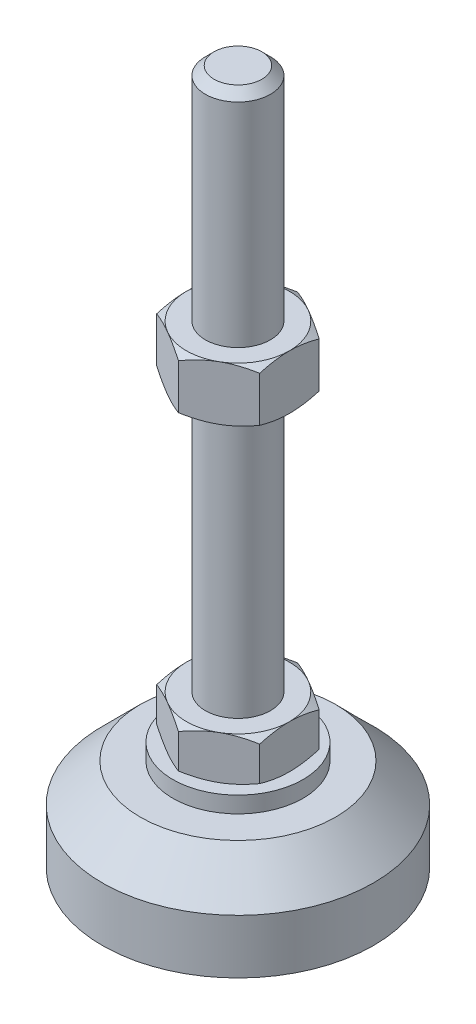
SolidWorks part; units mm, degrees
ref_plane "Спереди" through (0, 0, 0) normal (0, 0, 1) x (1, 0, 0)
ref_plane "Сверху" through (0, 0, 0) normal (0, 1, 0) x (1, 0, 0)
ref_plane "Справа" through (0, 0, 0) normal (1, 0, 0) x (0, 0, -1)
sketch "Эскиз1" plane through (0, 0, 0) normal (0, 0, 1) x (1, 0, 0)
  line L0 (0, 0) -> (-25, 0)
  line L3 (-25, 0) -> (-25, 10)
  line L5 (-12, 20) -> (-6, 20)
  line L12 (-6, 28) -> (-6, 126.4)
  line L13 (-6, 126.4) -> (-4.4, 128)
  line L14 (-4.4, 128) -> (0, 128)
  line L15 (0, 128) -> (0, 0) construction
  line L16 (-6, 20) -> (0, 20) construction
  line L17 (0, 0) -> (0, 128)
  line L18 (0, 0) -> (0, -7.9595) construction
  line L19 (-6, 28) -> (-6, 20)
  line L20 (-12, 20) -> (-12, 17)
  line L21 (-12, 17) -> (-18, 17)
  line L22 (-18, 17) -> (-25, 10)
  point P8 (-6, 77.2)
  point P23 (-9, 20)
  dimension "D1" = 12
  dimension "D2" = 20
  dimension "D3" = 8
  dimension "D4" = 50
  dimension "D5" = 6
  dimension "D6" = 1.6
  dimension "D7" = 45
  dimension "D8" = 24
  dimension "D10" = 100
  dimension "D11" = 10
  dimension "D12" = 45
  dimension "D13" = 3
revolve "Повернуть1" add sketch "Эскиз1" angle 360 about L17
sketch "Эскиз2" plane through (0, 20, 0) normal (0, 1, 0) x (1, 0, 0)
  line L1 (0, 10.9697) -> (-9.5, 5.4848)
  line L2 (-9.5, 5.4848) -> (-9.5, -5.4848)
  line L3 (-9.5, -5.4848) -> (0, -10.9697)
  line L4 (0, -10.9697) -> (9.5, -5.4848)
  line L5 (9.5, -5.4848) -> (9.5, 5.4848)
  line L6 (9.5, 5.4848) -> (0, 10.9697)
  circle A0 centre (0, 0) radius 9.5 construction
  dimension "D1" = 19
extrude "Бобышка-Вытянуть1" add sketch "Эскиз2" along normal up to vertex (8 mm away) up to point (-6, 28, 0)
ref_plane "Плоскость1" through (0, 77.2, 0) normal (0, 1, 0) x (1, 0, 0)
sketch "Эскиз3" plane through (0, 77.2, 0) normal (0, 1, 0) x (1, 0, 0)
  line L6 (9.5, 5.4848) -> (0, 10.9697)
  line L7 (0, 10.9697) -> (-9.5, 5.4848)
  line L8 (-9.5, 5.4848) -> (-9.5, -5.4848)
  line L9 (-9.5, -5.4848) -> (0, -10.9697)
  line L10 (0, -10.9697) -> (9.5, -5.4848)
  line L11 (9.5, -5.4848) -> (9.5, 5.4848)
  line L12 (9.5, 5.4848) -> (0, 10.9697)
  line L13 (0, 10.9697) -> (-9.5, 5.4848)
  line L14 (-9.5, 5.4848) -> (-9.5, -5.4848)
  line L15 (-9.5, -5.4848) -> (0, -10.9697)
  line L16 (0, -10.9697) -> (9.5, -5.4848)
  line L17 (9.5, -5.4848) -> (9.5, 5.4848)
  dimension "D1" = 0
extrude "Бобышка-Вытянуть2" add sketch "Эскиз3" along normal blind 10
sketch "Эскиз4" plane through (0, 0, 0) normal (0, 0, 1) x (1, 0, 0)
  line L0 (-9.5, 87.2) -> (-18.1603, 82.2)
  line L1 (-18.1603, 82.2) -> (-18.1603, 87.2)
  line L2 (-18.1603, 87.2) -> (-9.5, 87.2)
  line L3 (-18.1603, 82.2) -> (-9.5, 77.2)
  line L4 (50, 77.2) -> (-50, 77.2) construction
  line L5 (-9.5, 77.2) -> (-18.1603, 77.2)
  line L6 (-18.1603, 77.2) -> (-18.1603, 82.2)
  line L7 (-9.5, 87.2) -> (-9.5, 77.2) construction
  line L8 (-9.5, 28) -> (-16.4282, 28)
  line L9 (-16.4282, 28) -> (-16.4282, 24)
  line L10 (-16.4282, 24) -> (-9.5, 28)
  line L11 (-9.5, 20) -> (-16.4282, 24)
  line L12 (-16.4282, 24) -> (-16.4282, 20)
  line L13 (-16.4282, 20) -> (-9.5, 20)
  line L14 (0, 128) -> (0, 96.3793) construction
  dimension "D1" = 30
  dimension "D2" = 30
revolve "Вырез-Повернуть2" cut sketch "Эскиз4" angle 360 about L14
